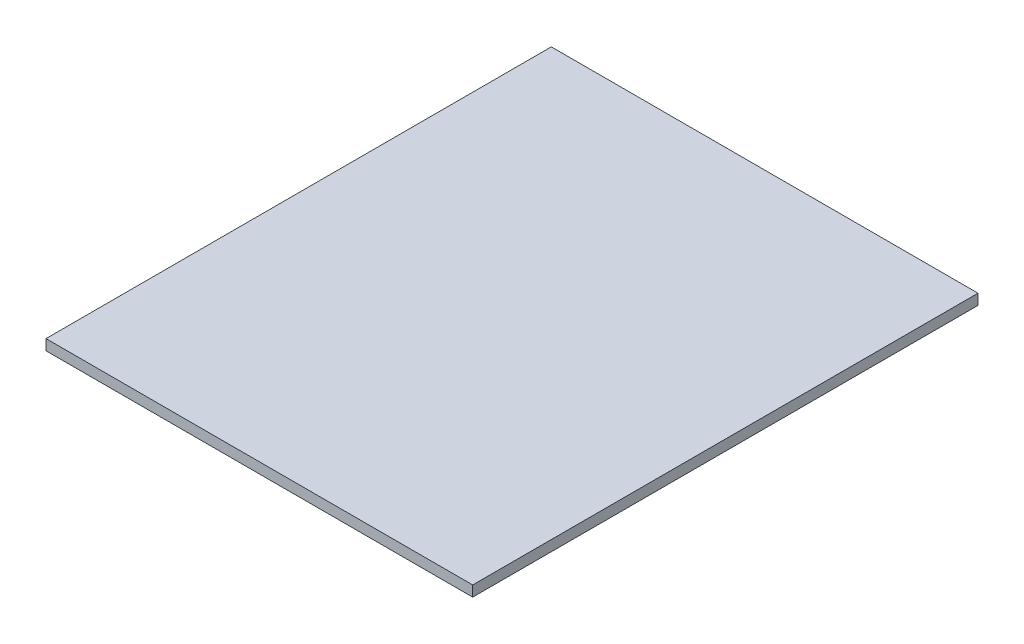
SolidWorks part; units mm, degrees
ref_plane "Front Plane" through (0, 0, 0) normal (0, 0, 1) x (1, 0, 0)
ref_plane "Top Plane" through (0, 0, 0) normal (0, 1, 0) x (1, 0, 0)
ref_plane "Right Plane" through (0, 0, 0) normal (1, 0, 0) x (0, 0, -1)
sketch "Sketch1" plane through (0, 0, 0) normal (0, 1, 0) x (1, 0, 0)
  line L1 (-60.452, -71.5899) -> (60.452, -71.5899)
  line L2 (-60.452, -71.5899) -> (-60.452, 71.5899)
  line L3 (-60.452, 71.5899) -> (60.452, 71.5899)
  line L4 (60.452, -71.5899) -> (60.452, 71.5899)
  line L5 (-60.452, -71.5899) -> (60.452, 71.5899) construction
  line L6 (-60.452, 71.5899) -> (60.452, -71.5899) construction
  point P0 (0, 0)
  dimension "D1" = 143.1798
  dimension "D2" = 120.904
extrude "Boss-Extrude1" add sketch "Sketch1" along normal mid plane 2.9972
